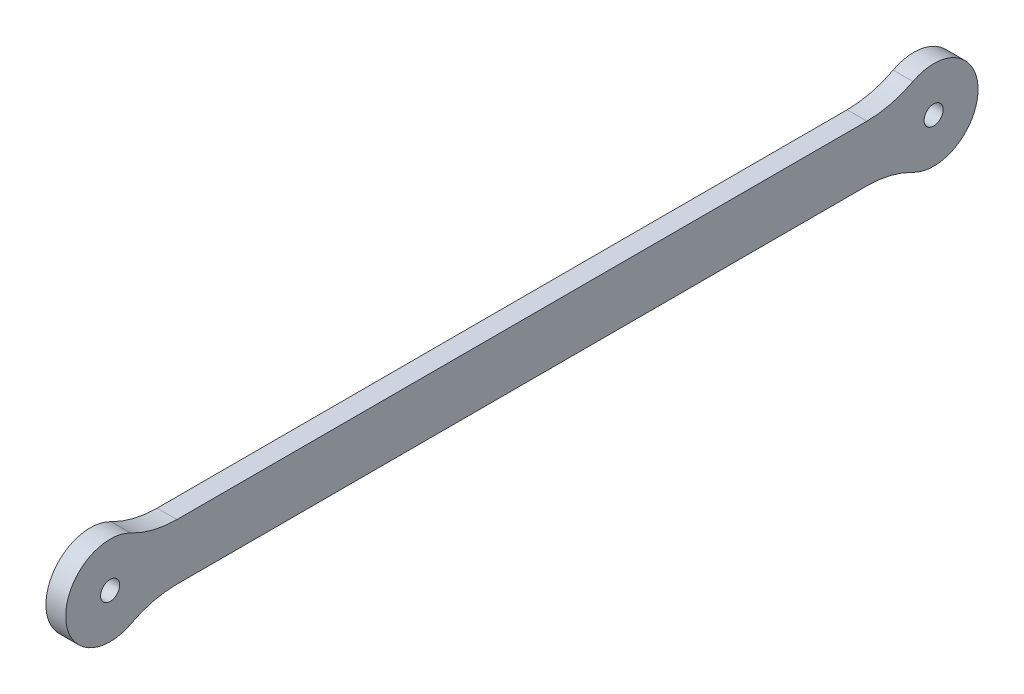
SolidWorks part; units mm, degrees
ref_plane "Front Plane" through (0, 0, 0) normal (0, 0, 1) x (1, 0, 0)
ref_plane "Top Plane" through (0, 0, 0) normal (0, 1, 0) x (1, 0, 0)
ref_plane "Right Plane" through (0, 0, 0) normal (1, 0, 0) x (0, 0, -1)
sketch "Sketch1" plane through (0, 0, 0) normal (1, 0, 0) x (0, 0, -1)
  line L0 (0, 0) -> (62.5, 0) construction
  line L1 (0, 0) -> (-62.5, 0) construction
  line L2 (0, 4.25) -> (0, -4.25) construction
  line L3 (57.256, -4.25) -> (-57.256, -4.25)
  line L4 (57.256, 4.25) -> (-57.256, 4.25)
  circle A0 centre (62.5, 0) radius 6.75
  circle A1 centre (-62.5, 0) radius 6.75
  circle A2 centre (-62.5, 0) radius 1.45
  circle A3 centre (62.5, 0) radius 1.45
  dimension "D2" = 13.5
  dimension "D3" = 2.9
  dimension "D1" = 125
  dimension "D4" = 8.5
extrude "Boss-Extrude1" add sketch "Sketch1" along normal mid plane 3 contours A1 A2 | A1 L3 A0 L4 | A0 A3
fillet "Fillet1" radius 15 4 edges at (0, 4.25, -57.256) (0, -4.25, -57.256) (0, -4.25, 57.256) (0, 4.25, 57.256)
